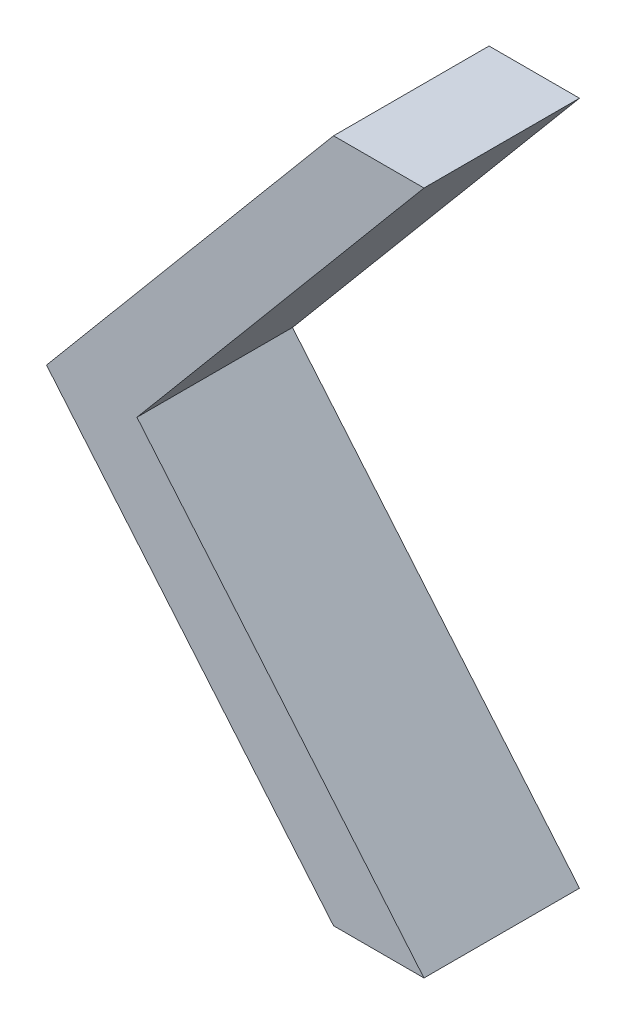
SolidWorks part; units mm, degrees
ref_plane "Front Plane" through (0, 0, 0) normal (0, 0, 1) x (1, 0, 0)
ref_plane "Top Plane" through (0, 0, 0) normal (0, 1, 0) x (1, 0, 0)
ref_plane "Right Plane" through (0, 0, 0) normal (1, 0, 0) x (0, 0, -1)
sketch "Sketch1" plane through (0, 0, 0) normal (0, 0, 1) x (1, 0, 0)
  line L0 (0, 0) -> (0, -69.9093) construction
  line L1 (0, 0) -> (-23.0752, -27.5)
  line L2 (-23.0752, -27.5) -> (0, -55)
  line L3 (0, 0) -> (7.27, 0)
  line L4 (0, -55) -> (7.27, -55)
  line L5 (7.27, 0) -> (-15.8052, -27.5)
  line L6 (-15.8052, -27.5) -> (7.27, -55)
  dimension "D1" = 100
  dimension "D2" = 55
  dimension "D3" = 7.27
  dimension "D4" = 7.27
extrude "Boss-Extrude1" add sketch "Sketch1" along normal blind 12.5
